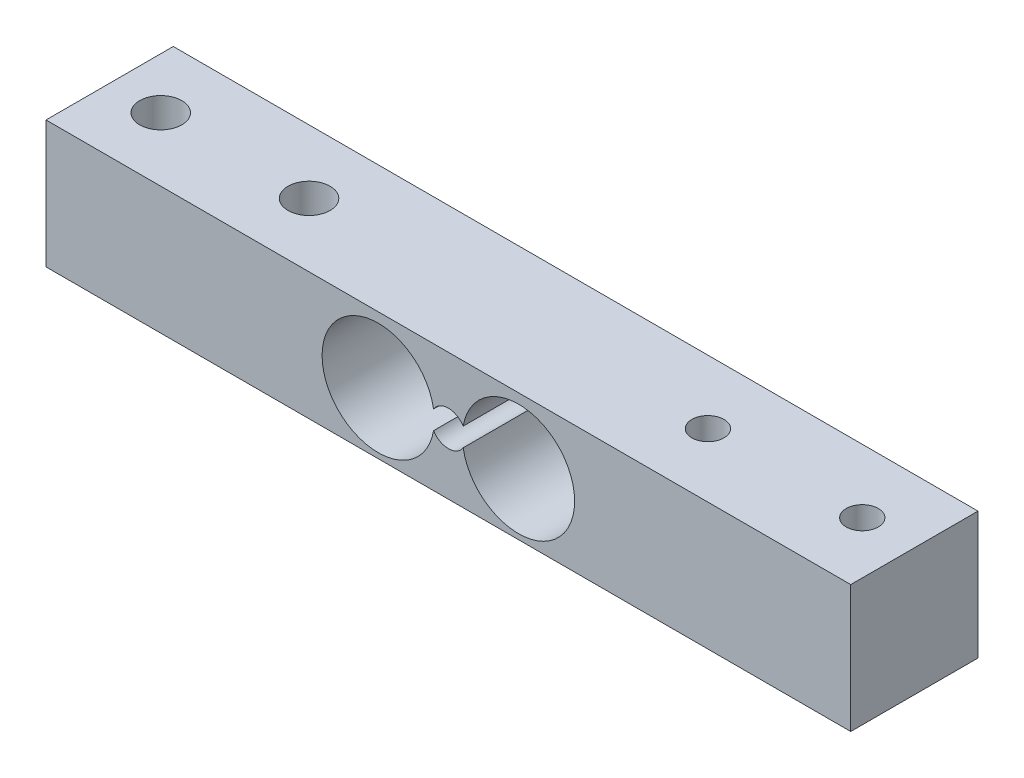
SolidWorks part; units mm, degrees
ref_plane "Plan de face" through (0, 0, 0) normal (0, 0, 1) x (1, 0, 0)
ref_plane "Plan de dessus" through (0, 0, 0) normal (0, 1, 0) x (1, 0, 0)
ref_plane "Plan de droite" through (0, 0, 0) normal (1, 0, 0) x (0, 0, -1)
sketch "Esquisse1" plane through (0, 0, 0) normal (0, 1, 0) x (1, 0, 0)
  line L1 (0, 0) -> (80.3, 0)
  line L2 (0, 0) -> (0, -12.7)
  line L3 (0, -12.7) -> (80.3, -12.7)
  line L4 (80.3, 0) -> (80.3, -12.7)
  dimension "D1" = 80.3
  dimension "D2" = 12.7
extrude "Boss.-Extru.1" add sketch "Esquisse1" along normal blind 12.7
sketch "Esquisse2" plane through (0, 12.7, 0) normal (0, 1, 0) x (1, 0, 0)
  line L0 (0, -6.35) -> (80.3, -6.35) construction
  line L1 (0, 0) -> (0, -12.7) construction
  line L2 (80.3, -12.7) -> (80.3, 0) construction
  circle A0 centre (5.1, -6.35) radius 2.1
  circle A1 centre (19.9, -6.35) radius 2.1
  circle A2 centre (59.7, -6.35) radius 1.6
  circle A3 centre (75.1, -6.35) radius 1.6
  dimension "D1" = 4.2
  dimension "D2" = 4.2
  dimension "D5" = 3.2
  dimension "D6" = 3.2
  dimension "D3" = 14.8
  dimension "D4" = 5.1
  dimension "D7" = 15.4
  dimension "D8" = 5.2
extrude "Enlèv. mat.-Extru.1" cut sketch "Esquisse2" against normal blind 12.7
sketch "Esquisse3" plane through (0, 0, 12.7) normal (0, 0, 1) x (1, 0, 0)
  line L0 (40.15, 12.7) -> (40.15, 0) construction
  line L1 (0, 12.7) -> (80.3, 12.7) construction
  line L2 (0, 0) -> (80.3, 0) construction
  arc A0 (38.6713, 7.0571) -> (38.6713, 5.1854) centre (33.15, 6.1212) ccw
  arc A1 (41.6287, 7.0571) -> (38.6713, 7.0571) centre (40.15, 6.1212) ccw
  arc A2 (41.6287, 5.1854) -> (41.6287, 7.0571) centre (47.15, 6.1212) ccw
  arc A3 (38.6713, 5.1854) -> (41.6287, 5.1854) centre (40.15, 6.1212) ccw
  dimension "D1" = 11.2
  dimension "D2" = 11.2
  dimension "D3" = 3.5
  dimension "D4" = 7
  dimension "D5" = 7
extrude "Enlèv. mat.-Extru.2" cut sketch "Esquisse3" against normal blind 12.7
equation "\"D2@Esquisse2\"=\"D1@Esquisse2\""
equation "\"D3@Esquisse2\"=19-4.2"
equation "\"D4@Esquisse2\"=3+\"D1@Esquisse2\"/2"
equation "\"D7@Esquisse2\"=18.6-\"D5@Esquisse2\""
equation "\"D6@Esquisse2\"=\"D5@Esquisse2\""
equation "\"D8@Esquisse2\"=3.6+\"D5@Esquisse2\"/2"
equation "\"D2@Esquisse3\"=\"D1@Esquisse3\""
equation "\"D5@Esquisse3\"=\"D4@Esquisse3\""
